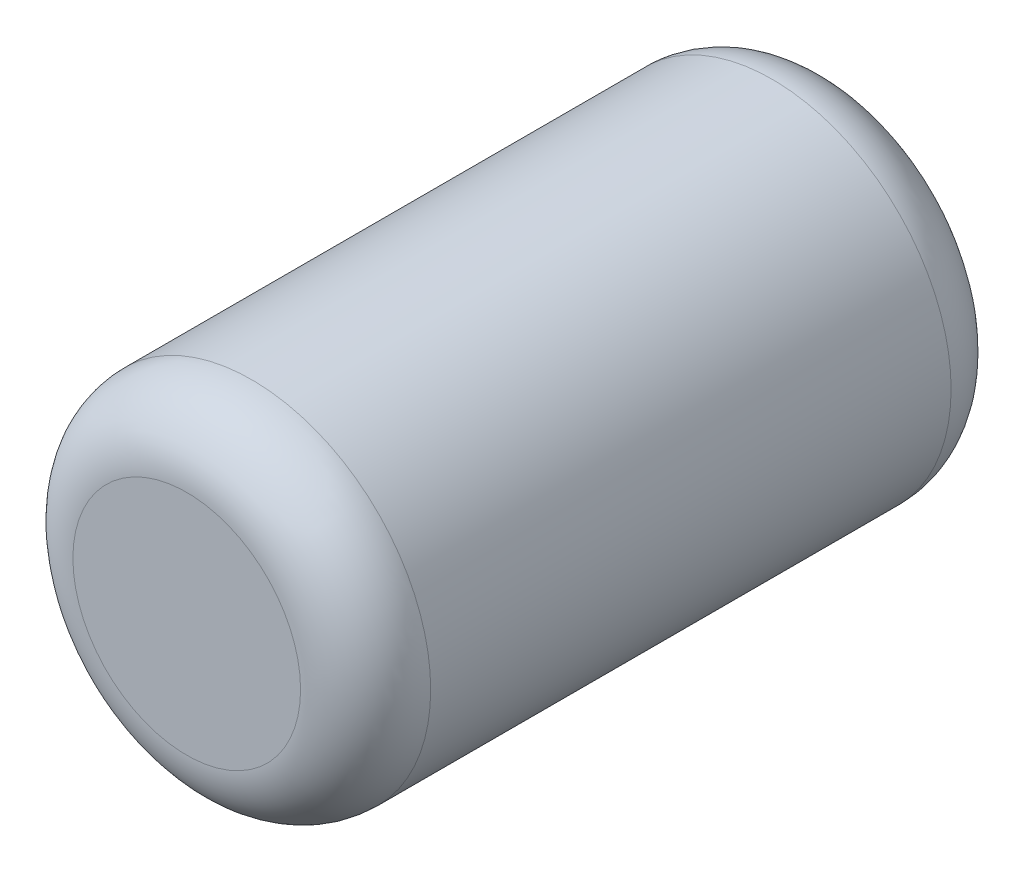
SolidWorks part; units mm, degrees
ref_plane "Front Plane" through (0, 0, 0) normal (0, 0, 1) x (1, 0, 0)
ref_plane "Top Plane" through (0, 0, 0) normal (0, 1, 0) x (1, 0, 0)
ref_plane "Right Plane" through (0, 0, 0) normal (1, 0, 0) x (0, 0, -1)
sketch "Sketch1" plane through (0, 0, 0) normal (0, 0, 1) x (1, 0, 0)
  circle A0 centre (0, 0) radius 34.925
  dimension "D1" = 69.85
extrude "Boss-Extrude1" add sketch "Sketch1" along normal blind 127 contours A0
fillet "Fillet2" radius 12.7 1 edges at (34.925, 0, 127)
fillet "Fillet3" radius 12.7 1 edges at (34.925, 0, 0)
